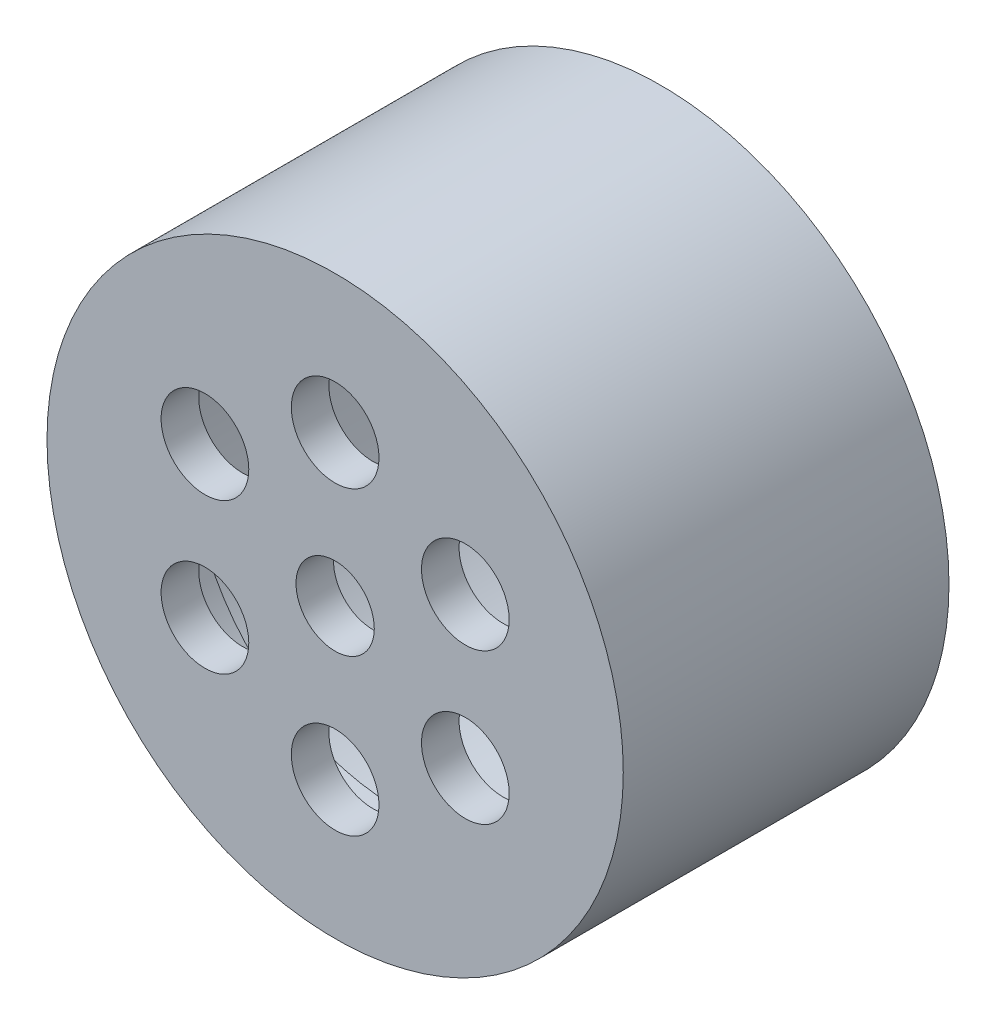
SolidWorks part; units mm, degrees
ref_plane "Alzado" through (0, 0, 0) normal (0, 0, 1) x (1, 0, 0)
ref_plane "Planta" through (0, 0, 0) normal (0, 1, 0) x (1, 0, 0)
ref_plane "Vista lateral" through (0, 0, 0) normal (1, 0, 0) x (0, 0, -1)
sketch "Croquis1" plane through (0, 0, 0) normal (0, 0, 1) x (1, 0, 0)
  circle A0 centre (0, 0) radius 23
  circle A1 centre (0, 0) radius 21
  dimension "D1" = 42
  dimension "D2" = 2
extrude "Saliente-Extruir1" add sketch "Croquis1" along normal blind 23
sketch "Croquis2" plane through (0, 0, 23) normal (0, 0, 1) x (1, 0, 0)
  circle A0 centre (0, 0) radius 3.125
  circle A1 centre (0, 0) radius 23
  circle A2 centre (0, 12) radius 3.5
  circle A3 centre (10.3923, 6) radius 3.5
  circle A4 centre (10.3923, -6) radius 3.5
  circle A5 centre (0, -12) radius 3.5
  circle A6 centre (-10.3923, -6) radius 3.5
  circle A7 centre (-10.3923, 6) radius 3.5
  circle A8 centre (0, 0) radius 23 construction
  dimension "D1" = 6.25
  dimension "D2" = 7
  dimension "D3" = 12
  dimension "D4" = 6
extrude "Saliente-Extruir2" add sketch "Croquis2" along normal blind 3
sketch "Croquis3" plane through (0, 0, 23) normal (0, 0, -1) x (-1, 0, 0)
  circle A7 centre (0, 0) radius 21
  circle A8 centre (0, 0) radius 16.5
  dimension "D1" = 33
extrude "Saliente-Extruir3" add sketch "Croquis3" along normal blind 2
